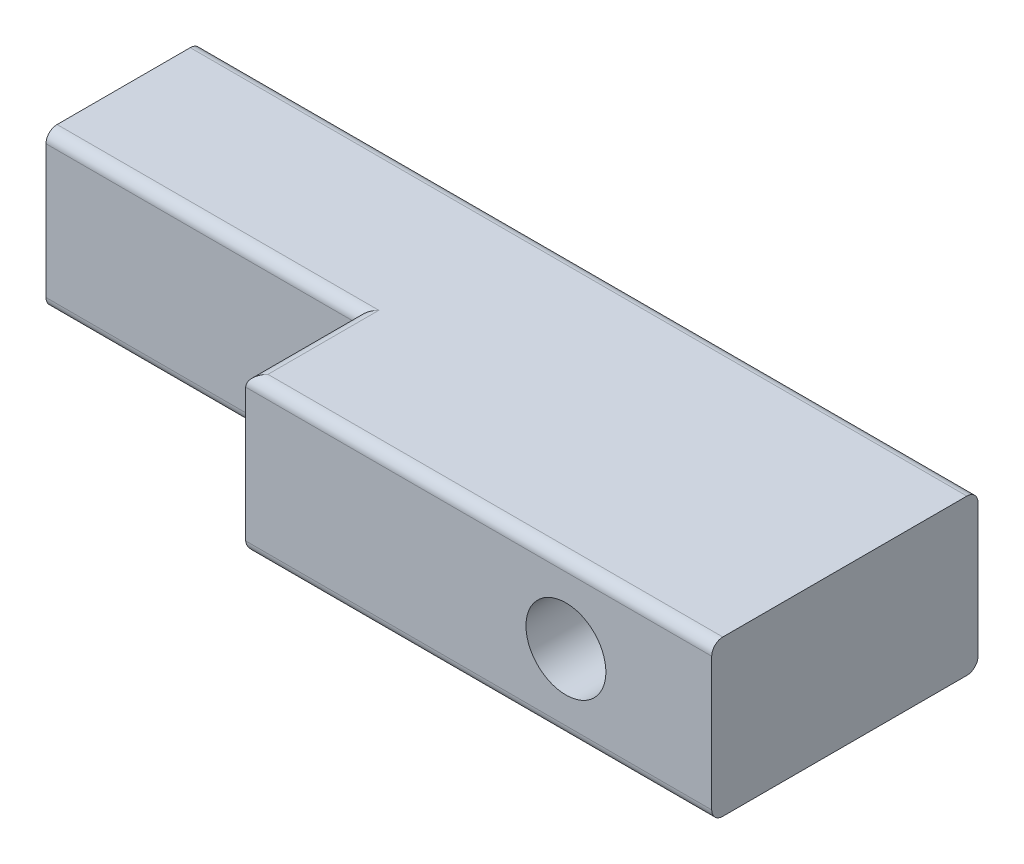
SolidWorks part; units mm, degrees
material "PLA"
ref_plane "Front Plane" through (0, 0, 0) normal (0, 0, 1) x (1, 0, 0)
ref_plane "Top Plane" through (0, 0, 0) normal (0, 1, 0) x (1, 0, 0)
ref_plane "Right Plane" through (0, 0, 0) normal (1, 0, 0) x (0, 0, -1)
sketch "Sketch1" plane through (0, 0, 0) normal (0, 0, 1) x (1, 0, 0)
  line L1 (-17.5, -3.5) -> (17.5, -3.5)
  line L2 (-17.5, -3.5) -> (-17.5, 3.5)
  line L3 (-17.5, 3.5) -> (17.5, 3.5)
  line L4 (17.5, -3.5) -> (17.5, 3.5)
  line L5 (-17.5, -3.5) -> (17.5, 3.5) construction
  line L6 (-17.5, 3.5) -> (17.5, -3.5) construction
  point P0 (0, 0)
  dimension "D1" = 35
  dimension "D2" = 7
extrude "Boss-Extrude1" add sketch "Sketch1" along normal blind 7
sketch "Sketch3" plane through (0, 0, 7) normal (0, 0, 1) x (1, 0, 0)
  line L0 (-17.5, -3.5) -> (17.5, -3.5) construction
  line L1 (17.5, 3.5) -> (-3.5, 3.5)
  line L2 (17.5, 3.5) -> (17.5, -3.5)
  line L3 (17.5, -3.5) -> (-3.5, -3.5)
  line L4 (-3.5, 3.5) -> (-3.5, -3.5)
  dimension "D1" = 21
extrude "Boss-Extrude3" add sketch "Sketch3" along normal blind 5
fillet "Fillet1" radius 0.5 8 edges at (-10.5, -3.5, 7) (-10.5, 3.5, 7) (7, -3.5, 12) (7, 3.5, 12) (0, -3.5, 0) (0, 3.5, 0) (-3.5, 3.5, 9.5) (-3.5, -3.5, 9.5)
sketch "Sketch5" plane through (0, 0, 0) normal (0, 0, -1) x (-1, 0, 0)
  circle A0 centre (-10.9296, 0) radius 1.5
  dimension "D1" = 3
hole_wizard "Ø3.6 (3.6) Diameter Hole1" positions "3DSketch1" profile "Sketch6" hole size "Ø3.6" standard "ANSI Metric" end condition through all
sketch3d "3DSketch1"
  point P0 (10.9296, 0, 0)
sketch "Sketch6" plane through (10.9296, 0, 0) normal (1, 0, 0) x (0, 1, 0)
  line L0 (0, 0) -> (0, 12)
  line L1 (0, 12) -> (1.8, 12)
  line L2 (1.8, 12) -> (1.8, 0)
  line L5 (1.8, 0) -> (0, 0)
  line L11 (0, -6.35) -> (0, 107.95) construction
  dimension "Thru Hole Dia." = 3.6
  dimension "Thru Hole Depth" = 12
